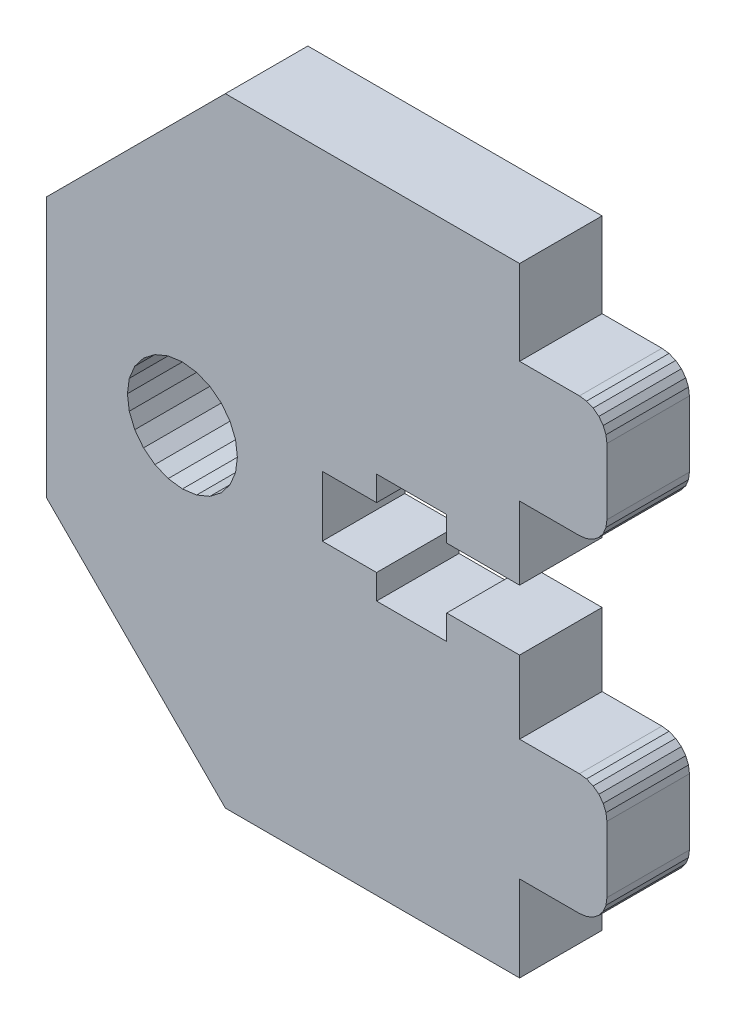
SolidWorks part; units mm, degrees
material "Maple"
ref_plane "Front Plane" through (0, 0, 0) normal (0, 0, 1) x (1, 0, 0)
ref_plane "Top Plane" through (0, 0, 0) normal (0, 1, 0) x (1, 0, 0)
ref_plane "Right Plane" through (0, 0, 0) normal (1, 0, 0) x (0, 0, -1)
sketch "Sketch1" plane through (0, 0, 0) normal (0, 0, 1) x (1, 0, 0)
  line L6195 (57.0628, -307.6435) -> (44.0628, -320.6435)
  line L6196 (78.4628, -352.6435) -> (78.4628, -346.4035)
  line L6197 (78.4628, -307.6435) -> (57.0628, -307.6435)
  line L6198 (44.0628, -339.6035) -> (44.0628, -320.6435)
  line L6199 (44.0628, -339.6035) -> (57.0628, -352.6435)
  line L6200 (84.8128, -320.6035) -> (84.8128, -315.8035)
  line L6201 (78.4628, -322.6035) -> (82.8128, -322.6035)
  line L6202 (82.8128, -313.8035) -> (78.4628, -313.8035)
  line L6203 (82.8128, -322.6035) -> (83.3304, -322.5353)
  line L6204 (83.8128, -322.3355) -> (84.227, -322.0177)
  line L6205 (83.3304, -322.5353) -> (83.8128, -322.3355)
  line L6206 (64.1128, -332.3035) -> (64.1128, -327.9035)
  line L6207 (73.1628, -326.1035) -> (73.1628, -327.9035)
  line L6208 (68.0628, -327.9035) -> (68.0628, -326.1035)
  line L6209 (84.227, -338.1893) -> (84.5448, -338.6035)
  line L6210 (68.0628, -334.1035) -> (68.0628, -332.3035)
  line L6211 (84.8128, -344.4035) -> (84.8128, -339.6035)
  line L6212 (84.5448, -345.4035) -> (84.7446, -344.9211)
  line L6213 (84.227, -345.8177) -> (84.5448, -345.4035)
  line L6214 (68.0628, -332.3035) -> (64.1128, -332.3035)
  line L6215 (83.8128, -346.1355) -> (84.227, -345.8177)
  line L6216 (83.3304, -346.3353) -> (83.8128, -346.1355)
  line L6217 (83.8128, -337.8714) -> (84.227, -338.1893)
  line L6218 (84.5448, -338.6035) -> (84.7446, -339.0859)
  line L6219 (83.3304, -337.6716) -> (83.8128, -337.8714)
  line L6220 (82.8128, -337.6035) -> (83.3304, -337.6716)
  line L6221 (82.8128, -337.6035) -> (78.4628, -337.6035)
  line L6222 (84.7446, -344.9211) -> (84.8128, -344.4035)
  line L6223 (82.8128, -346.4035) -> (83.3304, -346.3353)
  line L6224 (73.1628, -332.3035) -> (73.1628, -334.1035)
  line L6225 (64.1128, -327.9035) -> (68.0628, -327.9035)
  line L6226 (78.4628, -346.4035) -> (82.8128, -346.4035)
  line L6227 (68.0628, -326.1035) -> (73.1628, -326.1035)
  line L6228 (84.7446, -339.0859) -> (84.8128, -339.6035)
  line L6229 (83.3304, -313.8717) -> (83.8128, -314.0715)
  line L6230 (73.1628, -334.1035) -> (68.0628, -334.1035)
  line L6231 (84.7446, -321.1211) -> (84.8128, -320.6035)
  line L6232 (83.8128, -314.0715) -> (84.227, -314.3893)
  line L6233 (84.227, -314.3893) -> (84.5448, -314.8035)
  line L6234 (84.5448, -314.8035) -> (84.7446, -315.2859)
  line L6235 (84.227, -322.0177) -> (84.5448, -321.6035)
  line L6236 (84.5448, -321.6035) -> (84.7446, -321.1211)
  line L6237 (84.7446, -315.2859) -> (84.8128, -315.8035)
  line L6238 (78.4628, -332.3035) -> (73.1628, -332.3035)
  line L6239 (73.1628, -327.9035) -> (78.4628, -327.9035)
  line L6240 (82.8128, -313.8035) -> (83.3304, -313.8717)
  line L6241 (78.4628, -327.9035) -> (78.4628, -322.6035)
  line L6242 (78.4628, -337.6035) -> (78.4628, -332.3035)
  line L6243 (78.4628, -313.8035) -> (78.4628, -307.6435)
  line L6244 (49.9401, -330.1035) -> (50.0764, -331.1388)
  line L6245 (53.9401, -326.1035) -> (52.9048, -326.2398)
  line L6246 (57.8038, -331.1388) -> (57.9401, -330.1035)
  line L6247 (57.4042, -332.1035) -> (57.8038, -331.1388)
  line L6248 (50.476, -332.1035) -> (51.1116, -332.9319)
  line L6249 (57.8038, -329.0682) -> (57.4042, -328.1035)
  line L6250 (52.9048, -326.2398) -> (51.9401, -326.6394)
  line L6251 (52.9048, -333.9672) -> (53.9401, -334.1035)
  line L6252 (54.9753, -326.2398) -> (53.9401, -326.1035)
  line L6253 (51.1116, -327.2751) -> (50.476, -328.1035)
  line L6254 (57.4042, -328.1035) -> (56.7685, -327.2751)
  line L6255 (51.1116, -332.9319) -> (51.9401, -333.5676)
  line L6256 (50.476, -328.1035) -> (50.0764, -329.0682)
  line L6257 (50.0764, -329.0682) -> (49.9401, -330.1035)
  line L6258 (55.9401, -326.6394) -> (54.9753, -326.2398)
  line L6259 (56.7685, -327.2751) -> (55.9401, -326.6394)
  line L6260 (51.9401, -333.5676) -> (52.9048, -333.9672)
  line L6261 (56.7685, -332.9319) -> (57.4042, -332.1035)
  line L6262 (51.9401, -326.6394) -> (51.1116, -327.2751)
  line L6263 (54.9753, -333.9672) -> (55.9401, -333.5676)
  line L6264 (55.9401, -333.5676) -> (56.7685, -332.9319)
  line L6265 (53.9401, -334.1035) -> (54.9753, -333.9672)
  line L6266 (50.0764, -331.1388) -> (50.476, -332.1035)
  line L6267 (57.9401, -330.1035) -> (57.8038, -329.0682)
  line L8418 (57.0628, -352.6435) -> (78.4628, -352.6435)
  line L9371 (67.2743, -341.7338) -> (67.2743, -337.4259)
  line L9372 (67.2743, -337.4259) -> (67.2743, -341.7338)
  line L9373 (67.2743, -341.7338) -> (69.4035, -341.7338)
  line L9374 (69.4035, -341.7338) -> (67.2743, -341.7338)
extrude "Boss-Extrude1" add sketch "Sketch1" along normal blind 6
